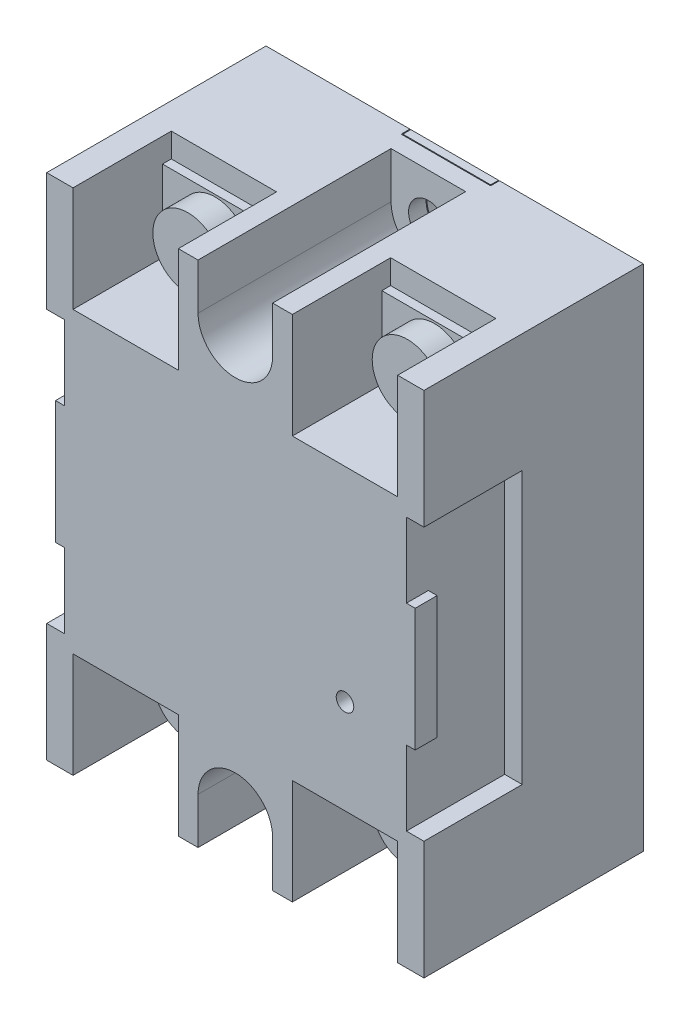
SolidWorks part; units mm, degrees
material "Polyester Resin"
ref_plane "Front Plane" through (0, 0, 0) normal (0, 0, 1) x (1, 0, 0)
ref_plane "Top Plane" through (0, 0, 0) normal (0, 1, 0) x (1, 0, 0)
ref_plane "Right Plane" through (0, 0, 0) normal (1, 0, 0) x (0, 0, -1)
ref_plane "Plane1" through (0, 0, 0) normal (0, 0, -1) x (-1, 0, 0)
sketch "Sketch1" plane through (0, 0, 0) normal (0, 0, -1) x (-1, 0, 0)
  line L0 (-5.1, 5.25) -> (-13.1, 5.25)
  line L1 (-13.1, 5.25) -> (-13.1, 3.85)
  line L2 (-13.1, 3.85) -> (-5.1, 3.85)
  line L3 (-5.1, 3.85) -> (-5.1, 5.25)
extrude "Boss-Extrude1" add sketch "Sketch1" against normal blind 1
ref_plane "Plane2" through (0, 0, 1) normal (0, 0, -1) x (-1, 0, 0)
sketch "Sketch2" plane through (0, 0, 1) normal (0, 0, -1) x (-1, 0, 0)
  line L0 (-13.1, 5.25) -> (-13.1, -52.75)
  line L1 (-13.1, -52.75) -> (21.5, -52.75)
  line L2 (21.5, -52.75) -> (21.5, 5.25)
  line L3 (21.5, 5.25) -> (-13.1, 5.25)
extrude "Boss-Extrude2" add sketch "Sketch2" against normal blind 24
sketch "Sketch3" plane through (0, 0, 1) normal (0, 0, -1) x (-1, 0, 0)
  line L0 (-13, -51.25) -> (-13, 3.75)
  line L1 (-13, 3.75) -> (13, 3.75)
  line L2 (13, 3.75) -> (13, -51.25)
  line L3 (13, -51.25) -> (-13, -51.25)
extrude "Boss-Extrude3" add sketch "Sketch3" along normal blind 1
sketch "Sketch4" plane through (0, 0, 1) normal (0, 0, -1) x (-1, 0, 0)
  line L0 (5.1, 5.25) -> (21.5, 5.25)
  line L1 (21.5, 5.25) -> (21.5, -52.75)
  line L2 (21.5, -52.75) -> (5.1, -52.75)
  line L3 (5.1, -52.75) -> (5.1, -51.35)
  line L4 (5.1, -51.35) -> (13.1, -51.35)
  line L5 (13.1, -51.35) -> (13.1, 3.85)
  line L6 (13.1, 3.85) -> (5.1, 3.85)
  line L7 (5.1, 3.85) -> (5.1, 5.25)
extrude "Boss-Extrude4" add sketch "Sketch4" along normal blind 1
sketch "Sketch5" plane through (0, 0, 1) normal (0, 0, -1) x (-1, 0, 0)
  line L0 (-13.1, -51.35) -> (-5.1, -51.35)
  line L1 (-5.1, -51.35) -> (-5.1, -52.75)
  line L2 (-5.1, -52.75) -> (-13.1, -52.75)
  line L3 (-13.1, -52.75) -> (-13.1, -51.35)
extrude "Boss-Extrude5" add sketch "Sketch5" along normal blind 1
ref_plane "Plane3" through (0, 0, 1) normal (0, 0, 1) x (1, 0, 0)
sketch "Sketch6" plane through (0, 0, 1) normal (0, 0, 1) x (1, 0, 0)
  line L0 (5.1, -4.75) -> (5.1, 3.75)
  line L1 (5.1, 3.75) -> (-5.1, 3.75)
  line L2 (-5.1, 3.75) -> (-5.1, -4.75)
  line L3 (-5.1, -4.75) -> (5.1, -4.75)
extrude "Cut-Extrude1" cut sketch "Sketch6" against normal blind 0.1
sketch "Sketch7" plane through (0, 0, 1) normal (0, 0, 1) x (1, 0, 0)
  line L0 (-5.1, -42.75) -> (-5.1, -51.25)
  line L1 (-5.1, -51.25) -> (5.1, -51.25)
  line L2 (5.1, -51.25) -> (5.1, -42.75)
  line L3 (5.1, -42.75) -> (-5.1, -42.75)
extrude "Cut-Extrude2" cut sketch "Sketch7" against normal blind 0.1
sketch "Sketch8" plane through (13.1, 0, 0) normal (1, 0, 0) x (0, 0, -1)
  line L0 (0, 5.25) -> (0, -52.75)
  line L1 (0, -52.75) -> (-25, -52.75)
  line L2 (-25, -52.75) -> (-25, 5.25)
  line L3 (-25, 5.25) -> (0, 5.25)
extrude "Boss-Extrude6" add sketch "Sketch8" along normal blind 8.4
sketch "Sketch9" plane through (0, -51.25, 0) normal (0, -1, 0) x (1, 0, 0)
  line L0 (5, 0.9) -> (5, 0)
  line L1 (5, 0) -> (-5, 0)
  line L2 (-5, 0) -> (-5, 0.9)
  line L3 (-5, 0.9) -> (5, 0.9)
extrude "Boss-Extrude7" add sketch "Sketch9" along normal blind 1.5
sketch "Sketch10" plane through (0, 3.75, 0) normal (0, 1, 0) x (-1, 0, 0)
  line L0 (5, 0.9) -> (5, 0)
  line L1 (5, 0) -> (-5, 0)
  line L2 (-5, 0) -> (-5, 0.9)
  line L3 (-5, 0.9) -> (5, 0.9)
extrude "Boss-Extrude8" add sketch "Sketch10" along normal blind 1.5
sketch "Sketch11" plane through (0, 5.25, 0) normal (0, 1, 0) x (-1, 0, 0)
  line L0 (-18.5, 25) -> (-18.5, 13.8)
  line L1 (-18.5, 13.8) -> (-6.5, 13.8)
  line L2 (-6.5, 13.8) -> (-6.5, 25)
  line L3 (-6.5, 25) -> (-18.5, 25)
extrude "Cut-Extrude3" cut sketch "Sketch11" against normal blind 12
sketch "Sketch12" plane through (6.5, 0, 0) normal (1, 0, 0) x (0, 0, -1)
  line L0 (-13.8, 2.5) -> (-13.8, -6)
  line L1 (-13.8, -6) -> (-14.8, -6)
  line L2 (-14.8, -6) -> (-14.8, 2.5)
  line L3 (-14.8, 2.5) -> (-13.8, 2.5)
extrude "Boss-Extrude9" add sketch "Sketch12" along normal blind 12
sketch "Sketch13" plane through (0, 5.25, 0) normal (0, 1, 0) x (-1, 0, 0)
  line L0 (6.5, 25) -> (6.5, 13.8)
  line L1 (6.5, 13.8) -> (18.5, 13.8)
  line L2 (18.5, 13.8) -> (18.5, 25)
  line L3 (18.5, 25) -> (6.5, 25)
extrude "Cut-Extrude4" cut sketch "Sketch13" against normal blind 12
sketch "Sketch14" plane through (-18.5, 0, 0) normal (1, 0, 0) x (0, 0, -1)
  line L0 (-13.8, 2.5) -> (-13.8, -6)
  line L1 (-13.8, -6) -> (-14.8, -6)
  line L2 (-14.8, -6) -> (-14.8, 2.5)
  line L3 (-14.8, 2.5) -> (-13.8, 2.5)
extrude "Boss-Extrude10" add sketch "Sketch14" along normal blind 12
sketch "Sketch15" plane through (0, -52.75, 0) normal (0, -1, 0) x (1, 0, 0)
  line L0 (6.5, 25) -> (6.5, 13.8)
  line L1 (6.5, 13.8) -> (18.5, 13.8)
  line L2 (18.5, 13.8) -> (18.5, 25)
  line L3 (18.5, 25) -> (6.5, 25)
extrude "Cut-Extrude5" cut sketch "Sketch15" against normal blind 12
sketch "Sketch16" plane through (18.5, 0, 0) normal (-1, 0, 0) x (0, 0, 1)
  line L0 (13.8, -50) -> (13.8, -41.5)
  line L1 (13.8, -41.5) -> (14.8, -41.5)
  line L2 (14.8, -41.5) -> (14.8, -50)
  line L3 (14.8, -50) -> (13.8, -50)
extrude "Boss-Extrude11" add sketch "Sketch16" along normal blind 12
sketch "Sketch17" plane through (0, -52.75, 0) normal (0, -1, 0) x (1, 0, 0)
  line L0 (-18.5, 25) -> (-18.5, 13.8)
  line L1 (-18.5, 13.8) -> (-6.5, 13.8)
  line L2 (-6.5, 13.8) -> (-6.5, 25)
  line L3 (-6.5, 25) -> (-18.5, 25)
extrude "Cut-Extrude6" cut sketch "Sketch17" against normal blind 12
sketch "Sketch18" plane through (-6.5, 0, 0) normal (-1, 0, 0) x (0, 0, 1)
  line L0 (13.8, -50) -> (13.8, -41.5)
  line L1 (13.8, -41.5) -> (14.8, -41.5)
  line L2 (14.8, -41.5) -> (14.8, -50)
  line L3 (14.8, -50) -> (13.8, -50)
extrude "Boss-Extrude12" add sketch "Sketch18" along normal blind 12
sketch "Sketch19" plane through (0, 0, 25) normal (0, 0, 1) x (1, 0, 0)
  line L0 (4.25, -52.75) -> (4.25, -47.5)
  line L1 (-4.25, -47.5) -> (-4.25, -52.75)
  line L2 (-4.25, -52.75) -> (4.25, -52.75)
  arc A0 (4.25, -47.5) -> (-4.25, -47.5) centre (0, -47.5) ccw
extrude "Cut-Extrude7" cut sketch "Sketch19" against normal blind 22
sketch "Sketch20" plane through (0, 0, 1) normal (0, 0, -1) x (-1, 0, 0)
  line L0 (-2.25, -52.75) -> (2.25, -52.75)
  line L1 (2.25, -52.75) -> (2.25, -47.5)
  line L2 (-2.25, -47.5) -> (-2.25, -52.75)
  arc A0 (2.25, -47.5) -> (-2.25, -47.5) centre (0, -47.5) ccw
extrude "Cut-Extrude8" cut sketch "Sketch20" against normal through all
sketch "Sketch21" plane through (0, 0, 0.9) normal (0, 0, 1) x (1, 0, 0)
  line L0 (-2.25, -52.75) -> (2.25, -52.75)
  line L1 (2.25, -52.75) -> (2.25, -47.5)
  line L2 (-2.25, -47.5) -> (-2.25, -52.75)
  arc A0 (2.25, -47.5) -> (-2.25, -47.5) centre (0, -47.5) ccw
extrude "Cut-Extrude9" cut sketch "Sketch21" against normal through all
sketch "Sketch22" plane through (21.5, 0, 0) normal (1, 0, 0) x (0, 0, -1)
  line L0 (-25, -39.25) -> (-13.8, -39.25)
  line L1 (-13.8, -39.25) -> (-13.8, -8.25)
  line L2 (-13.8, -8.25) -> (-25, -8.25)
  line L3 (-25, -8.25) -> (-25, -39.25)
extrude "Cut-Extrude10" cut sketch "Sketch22" against normal blind 2
sketch "Sketch23" plane through (19.5, 0, 0) normal (1, 0, 0) x (0, 0, -1)
  line L0 (-25, -30.75) -> (-25, -16.75)
  line L1 (-25, -16.75) -> (-22.5, -16.75)
  line L2 (-22.5, -16.75) -> (-22.5, -30.75)
  line L3 (-22.5, -30.75) -> (-25, -30.75)
extrude "Boss-Extrude13" add sketch "Sketch23" along normal blind 1
sketch "Sketch24" plane through (-21.5, 0, 0) normal (-1, 0, 0) x (0, 0, 1)
  line L0 (25, -8.25) -> (13.8, -8.25)
  line L1 (13.8, -8.25) -> (13.8, -39.25)
  line L2 (13.8, -39.25) -> (25, -39.25)
  line L3 (25, -39.25) -> (25, -8.25)
extrude "Cut-Extrude11" cut sketch "Sketch24" against normal blind 2
sketch "Sketch25" plane through (-19.5, 0, 0) normal (-1, 0, 0) x (0, 0, 1)
  line L0 (25, -16.75) -> (25, -30.75)
  line L1 (25, -30.75) -> (22.5, -30.75)
  line L2 (22.5, -30.75) -> (22.5, -16.75)
  line L3 (22.5, -16.75) -> (25, -16.75)
extrude "Boss-Extrude14" add sketch "Sketch25" along normal blind 1
sketch "Sketch26" plane through (0, 0, 25) normal (0, 0, 1) x (1, 0, 0)
  line L0 (-4.25, 5.25) -> (-4.25, 0)
  line L1 (4.25, 0) -> (4.25, 5.25)
  line L2 (4.25, 5.25) -> (-4.25, 5.25)
  arc A0 (-4.25, 0) -> (4.25, 0) centre (0, 0) ccw
extrude "Cut-Extrude12" cut sketch "Sketch26" against normal blind 22
ref_plane "Plane4" through (0, -45.75, 0) normal (0, -1, 0) x (1, 0, 0)
sketch "Sketch27" plane through (0, -45.75, 0) normal (0, -1, 0) x (1, 0, 0)
  line L0 (16.5, 17.9) -> (12.5, 17.9)
  line L1 (12.5, 17.9) -> (12.5, 14.8)
  line L2 (12.5, 14.8) -> (16.5, 14.8)
  line L3 (16.5, 14.8) -> (16.5, 17.9)
  line L4 (12.5, 17.9) -> (12.5, 14.8) construction
revolve "Revolve1" add sketch "Sketch27" angle 360 about L4
ref_plane "Plane5" through (0, -1.75, 0) normal (0, -1, 0) x (1, 0, 0)
sketch "Sketch28" plane through (0, -1.75, 0) normal (0, -1, 0) x (1, 0, 0)
  line L0 (16.5, 17.9) -> (12.5, 17.9)
  line L1 (12.5, 17.9) -> (12.5, 14.8)
  line L2 (12.5, 14.8) -> (16.5, 14.8)
  line L3 (16.5, 14.8) -> (16.5, 17.9)
  line L4 (12.5, 17.9) -> (12.5, 14.8) construction
revolve "Revolve2" add sketch "Sketch28" angle 360 about L4
sketch "Sketch29" plane through (0, -45.75, 0) normal (0, -1, 0) x (1, 0, 0)
  line L0 (-8.5, 17.9) -> (-12.5, 17.9)
  line L1 (-12.5, 17.9) -> (-12.5, 14.8)
  line L2 (-12.5, 14.8) -> (-8.5, 14.8)
  line L3 (-8.5, 14.8) -> (-8.5, 17.9)
  line L4 (-12.5, 17.9) -> (-12.5, 14.8) construction
revolve "Revolve3" add sketch "Sketch29" angle 360 about L4
sketch "Sketch30" plane through (0, -1.75, 0) normal (0, -1, 0) x (1, 0, 0)
  line L0 (-8.5, 17.9) -> (-12.5, 17.9)
  line L1 (-12.5, 17.9) -> (-12.5, 14.8)
  line L2 (-12.5, 14.8) -> (-8.5, 14.8)
  line L3 (-8.5, 14.8) -> (-8.5, 17.9)
  line L4 (-12.5, 17.9) -> (-12.5, 14.8) construction
revolve "Revolve4" add sketch "Sketch30" angle 360 about L4
hole_wizard "Ø2.0 (2) Diameter Hole1" positions "Sketch32" profile "Sketch31" hole size "Ø2.0" standard "ANSI Metric"
sketch "Sketch32" plane through (0, 0, 25) normal (0, 0, 1) x (1, 0, 0)
  point P0 (12.5, -30)
sketch "Sketch31" plane through (12.5, -30, 25) normal (1, 0, 0) x (0, -1, 0)
  line L0 (0, 0) -> (0, 1.5)
  line L1 (0, 1.5) -> (1, 1.5)
  line L2 (1, 1.5) -> (1, 0)
  line L5 (1, 0) -> (0, 0)
  line L10 (0, 1.5) -> (-1, 1.5) construction
  line L11 (0, -6.35) -> (0, 107.95) construction
  dimension "Hole Dia." = 2
  dimension "Hole Depth" = 1.5
  dimension "Drill Angle" = 180
hole_wizard "Ø4.5 (4.5) Diameter Hole1" positions "Sketch34" profile "Sketch33" hole size "Ø4.5" standard "ANSI Metric"
sketch "Sketch34" plane through (0, 0, 0) normal (0, 0, -1) x (-1, 0, 0)
  point P0 (0, 0)
sketch "Sketch33" plane through (0, 0, 0) normal (1, 0, 0) x (0, 1, 0)
  line L0 (0, 0) -> (0, 0.9)
  line L1 (0, 0.9) -> (2.25, 0.9)
  line L2 (2.25, 0.9) -> (2.25, 0)
  line L5 (2.25, 0) -> (0, 0)
  line L11 (0, -6.35) -> (0, 107.95) construction
  dimension "Thru Hole Dia." = 4.5
  dimension "Thru Hole Depth" = 0.9
hole_wizard "Ø4.5 (4.5) Diameter Hole2" positions "Sketch36" profile "Sketch35" hole size "Ø4.5" standard "ANSI Metric"
sketch "Sketch36" plane through (0, 0, 1) normal (0, 0, -1) x (-1, 0, 0)
  point P0 (0, 0)
sketch "Sketch35" plane through (0, 0, 1) normal (1, 0, 0) x (0, 1, 0)
  line L0 (0, 0) -> (0, 24)
  line L1 (0, 24) -> (2.25, 24)
  line L2 (2.25, 24) -> (2.25, 0)
  line L5 (2.25, 0) -> (0, 0)
  line L11 (0, -6.35) -> (0, 107.95) construction
  dimension "Thru Hole Dia." = 4.5
  dimension "Thru Hole Depth" = 24
